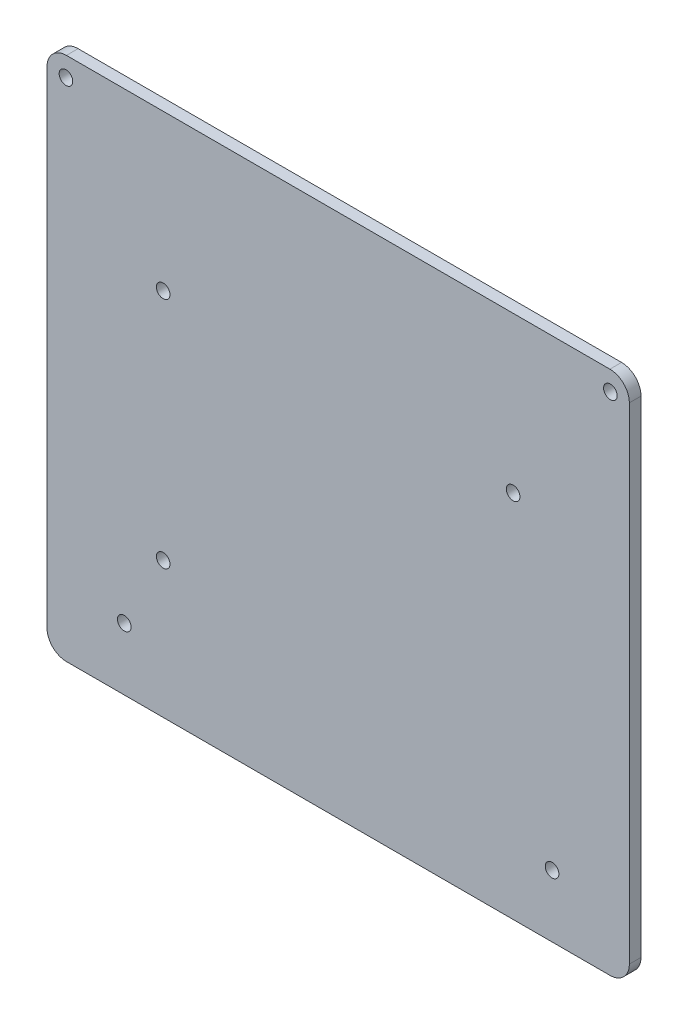
SolidWorks part; units mm, degrees
ref_plane "Plan de face" through (0, 0, 0) normal (0, 0, 1) x (1, 0, 0)
ref_plane "Plan de dessus" through (0, 0, 0) normal (0, 1, 0) x (1, 0, 0)
ref_plane "Plan de droite" through (0, 0, 0) normal (1, 0, 0) x (0, 0, -1)
sketch "Esquisse1" plane through (0, 0, 0) normal (0, 0, 1) x (1, 0, 0)
  line L0 (55, -67.5) -> (55, -51.5) construction
  line L1 (-74.875, 67.5) -> (74.875, 67.5)
  line L2 (-74.875, 67.5) -> (-74.875, -67.5)
  line L3 (-74.875, -67.5) -> (74.875, -67.5)
  line L4 (74.875, 67.5) -> (74.875, -67.5)
  line L5 (55, -51.5) -> (74.875, -51.5) construction
  line L6 (0, 0) -> (0, -67.5) construction
  line L7 (70, 62.5) -> (-70, 62.5) construction
  line L8 (-45, -32.5) -> (-55, -32.5) construction
  line L9 (-55, -32.5) -> (-55, -51.5) construction
  line L11 (-45, -32.5) -> (-45, 27.5) construction
  line L12 (-45, 27.5) -> (45, 27.5) construction
  line L13 (45, 27.5) -> (45, -2.5) construction
  circle A6 centre (-70, 62.5) radius 1.75
  circle A7 centre (70, 62.5) radius 1.75
  circle A8 centre (55, -51.5) radius 1.75
  circle A9 centre (-55, -51.5) radius 1.75
  circle A10 centre (45, -2.5) radius 1.75 construction
  circle A11 centre (45, 27.5) radius 1.75
  circle A12 centre (-45, 27.5) radius 1.75
  circle A13 centre (-45, -32.5) radius 1.75
  point P4 (0, 67.5)
  point P5 (-74.875, 0)
  point P26 (0, 62.5)
  point P32 (0, 27.5)
  dimension "D5" = 16
  dimension "D9" = 5
  dimension "D3" = 3.5
  dimension "D1" = 135
  dimension "D2" = 149.75
  dimension "D4" = 19.875
  dimension "D7" = 60
  dimension "D8" = 140
  dimension "D10" = 19
  dimension "D11" = 90
  dimension "D6" = 30
extrude "Boss.-Extru.1" add sketch "Esquisse1" along normal blind 3
fillet "Congé1" radius 5 4 edges at (74.875, -67.5, 1.5) (-74.875, -67.5, 1.5) (-74.875, 67.5, 1.5) (74.875, 67.5, 1.5)
